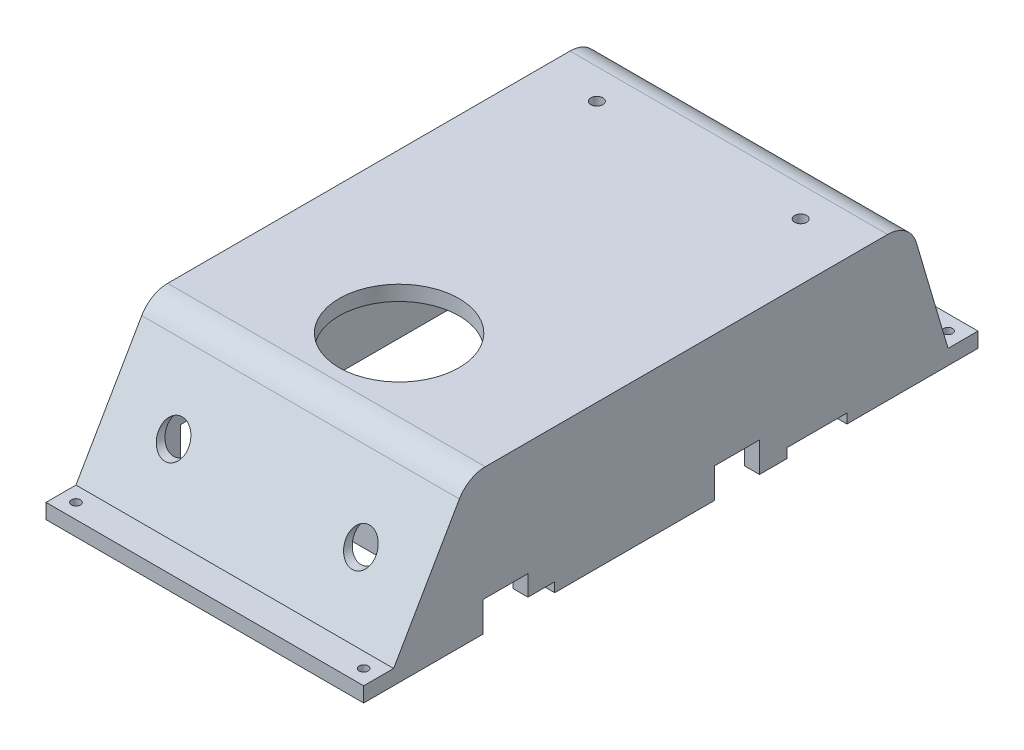
SolidWorks part; units mm, degrees
ref_plane "Front Plane" through (0, 0, 0) normal (0, 0, 1) x (1, 0, 0)
ref_plane "Top Plane" through (0, 0, 0) normal (0, 1, 0) x (1, 0, 0)
ref_plane "Right Plane" through (0, 0, 0) normal (1, 0, 0) x (0, 0, -1)
sketch "Sketch1" plane through (0, 0, 0) normal (0, 1, 0) x (1, 0, 0)
  line L1 (-78, -130) -> (78, -130)
  line L2 (-78, -130) -> (-78, 130)
  line L3 (-78, 130) -> (78, 130)
  line L4 (78, -130) -> (78, 130)
  line L5 (-78, -130) -> (78, 130) construction
  line L6 (-78, 130) -> (78, -130) construction
  point P1 (0, 0)
  dimension "D1" = 156
  dimension "D2" = 260
extrude "Boss-Extrude1" add sketch "Sketch1" along normal blind 10
sketch "Sketch2" plane through (0, 0, 0) normal (0, -1, 0) x (1, 0, 0)
  line L0 (78, 130) -> (78, -130) construction
  line L1 (-73, -120) -> (73, -120) construction
  line L2 (-73, -120) -> (-73, 125)
  line L3 (-73, 125) -> (73, 125)
  line L4 (73, -120) -> (73, 125)
  line L5 (78, -130) -> (-78, -130) construction
  line L7 (-78, -130) -> (-78, 130) construction
  line L8 (-78, 130) -> (78, 130) construction
  line L9 (78, 130) -> (78, -120)
  line L10 (-78, -120) -> (-78, 130)
  line L11 (-78, 130) -> (78, 130)
  line L12 (-73, -120) -> (-78, -120)
  line L13 (73, -120) -> (78, -120)
  point P0 (0, 0)
  dimension "D1" = 5
  dimension "D2" = 5
  dimension "D3" = 10
  dimension "D4" = 5
extrude "Boss-Extrude2" add sketch "Sketch2" along normal blind 66
sketch "Sketch3" plane through (0, 10, 0) normal (0, 1, 0) x (1, 0, 0)
  line L0 (-78, 130) -> (-78, -130) construction
  line L2 (-73, -125) -> (73, -125) construction
  circle A0 centre (0, -70) radius 40
  dimension "D2" = 80
  dimension "D1" = 55
  dimension "D3" = 78
extrude "Cut-Extrude1" cut sketch "Sketch3" against normal through all
sketch "Sketch4" plane through (0, 0, 130) normal (0, 0, 1) x (1, 0, 0)
  line L0 (0, 10) -> (0, -66) construction
  line L1 (-78, 10) -> (78, 10) construction
  line L2 (78, -66) -> (-78, -66) construction
  line L3 (-72.5, -28.5) -> (-52.5, -28.5)
  line L4 (-52.5, -28.5) -> (-52.5, -66)
  line L5 (-52.5, -66) -> (-72.5, -66)
  line L6 (-72.5, -66) -> (-72.5, -28.5)
  line L7 (52.5, -66) -> (72.5, -66)
  line L8 (52.5, -28.5) -> (52.5, -66)
  line L9 (72.5, -28.5) -> (52.5, -28.5)
  line L10 (72.5, -66) -> (72.5, -28.5)
  line L11 (-78, 10) -> (-78, -66) construction
  dimension "D1" = 20
  dimension "D2" = 37.5
  dimension "D3" = 5.5
extrude "Cut-Extrude2" cut sketch "Sketch4" against normal blind 5
sketch "Sketch6" plane through (0, -66, 0) normal (0, -1, 0) x (1, 0, 0)
  line L0 (78, 130) -> (72.5, 130) construction
  line L1 (-7.5, 145) -> (7.5, 145)
  line L2 (-7.5, 145) -> (-7.5, 130)
  line L3 (-7.5, 130) -> (7.5, 130)
  line L4 (7.5, 145) -> (7.5, 130)
  line L5 (-7.5, 145) -> (7.5, 130) construction
  line L6 (-7.5, 130) -> (7.5, 145) construction
  line L7 (-78, 130) -> (-78, -120) construction
  point P0 (0, 137.5)
  dimension "D1" = 15
  dimension "D2" = 15
  dimension "D3" = 78
extrude "Boss-Extrude3" add sketch "Sketch6" against normal blind 10
sketch "Sketch7" plane through (0, -66, 0) normal (0, -1, 0) x (1, 0, 0)
  line L0 (7.5, 145) -> (-7.5, 145) construction
  line L1 (-7.5, 145) -> (-7.5, 130) construction
  circle A0 centre (0, 137.5) radius 4
  dimension "D1" = 8
  dimension "D2" = 7.5
  dimension "D3" = 7.5
extrude "Cut-Extrude4" cut sketch "Sketch7" against normal blind 10
fillet "Fillet1" radius 2 2 edges at (7.5, -61, 145) (-7.5, -61, 145)
sketch "Sketch8" plane through (0, 0, -130) normal (0, 0, -1) x (-1, 0, 0)
  line L4 (-78, 0) -> (78, 0)
  line L5 (78, 0) -> (78, 10)
  line L6 (78, 10) -> (-78, 10)
  line L9 (78, 0) -> (78, 10)
  line L10 (78, 10) -> (-78, 10)
  line L12 (-78, 0) -> (78, 0)
  line L14 (-78, 10) -> (-78, 0)
  line L15 (-78, 10) -> (-78, 0)
  dimension "D1" = 0
extrude "Boss-Extrude4" add sketch "Sketch8" along normal blind 10
sketch "Sketch9" plane through (0, 10, 0) normal (0, 1, 0) x (1, 0, 0)
  line L0 (-78, 140) -> (78, 140) construction
  line L1 (-78, 140) -> (-78, -130) construction
  line L2 (78, -130) -> (78, 140) construction
  circle A0 centre (-68, 130) radius 4
  circle A1 centre (68, 130) radius 4
  dimension "D1" = 8
  dimension "D6" = 8
  dimension "D2" = 10
  dimension "D3" = 10
  dimension "D4" = 10
  dimension "D5" = 10
extrude "Cut-Extrude5" cut sketch "Sketch9" against normal through all
sketch "Sketch10" plane through (0, 0, -140) normal (0, 0, -1) x (-1, 0, 0)
  line L4 (-78, 10) -> (-78, 0)
  line L5 (-78, 0) -> (78, 0)
  line L6 (78, 0) -> (78, 10)
  line L7 (78, 10) -> (-78, 10)
  line L8 (-78, 10) -> (-78, 0)
  line L9 (-78, 0) -> (78, 0)
  line L10 (78, 0) -> (78, 10)
  line L11 (78, 10) -> (-78, 10)
  dimension "D1" = 0
extrude "Boss-Extrude5" add sketch "Sketch10" along normal blind 25
sketch "Sketch11" plane through (0, 10, 0) normal (0, 1, 0) x (1, 0, 0)
  line L0 (0, -145) -> (0, 165) construction
  line L1 (-78, 165) -> (-106, 165)
  line L2 (-78, 165) -> (-78, -130)
  line L3 (-78, -130) -> (-106, -130)
  line L4 (-106, 165) -> (-106, -130)
  line L5 (5.5, -145) -> (-5.5, -145) construction
  line L6 (-78, 165) -> (78, 165) construction
  line L7 (78, -130) -> (106, -130)
  line L8 (106, 165) -> (106, -130)
  line L9 (78, 165) -> (106, 165)
  line L10 (78, 165) -> (78, -130)
  dimension "D1" = 28
  dimension "D2" = 295
extrude "Boss-Extrude6" add sketch "Sketch11" against normal up to surface (10 mm away) up to face at (-68, 0, -134)
sketch "Sketch12" plane through (-106, 0, 0) normal (-1, 0, 0) x (0, 0, 1)
  line L0 (-165, 0) -> (-190.35, -86)
  line L1 (-165, 0) -> (130, 0) construction
  line L2 (-190.35, -86) -> (-210.35, -86)
  line L3 (-210.35, -86) -> (-210.35, -76)
  line L4 (-165, 10) -> (-190.35, -76)
  line L5 (-190.35, -76) -> (-210.35, -76)
  line L8 (-165, 10) -> (-165, 0)
  dimension "D1" = 73.576
  dimension "D2" = 86
  dimension "D3" = 10
  dimension "D4" = 20
  dimension "D5" = 20
extrude "Boss-Extrude7" add sketch "Sketch12" against normal up to surface (212 mm away) up to face at (106, 5, -17.5)
sketch "Sketch13" plane through (0, -76, 0) normal (0, 1, 0) x (1, 0, 0)
  line L0 (-106, 190.35) -> (-106, 210.35) construction
  line L1 (0, 210.35) -> (0, 190.35) construction
  line L2 (106, 210.35) -> (-106, 210.35) construction
  line L3 (106, 190.35) -> (-106, 190.35) construction
  circle A0 centre (-96, 200.35) radius 3
  circle A1 centre (96, 200.35) radius 3
  dimension "D2" = 6
  dimension "D1" = 10
  dimension "D3" = 10
extrude "Cut-Extrude6" cut sketch "Sketch13" against normal through all
sketch "Sketch17" plane through (106, 0, 0) normal (1, 0, 0) x (0, 0, -1)
  line L0 (-130, 0) -> (-179.6521, -86)
  line L1 (120, 0) -> (-130, 0) construction
  line L2 (-179.6521, -86) -> (-199.6521, -86)
  line L3 (-199.6521, -86) -> (-199.6521, -76)
  line L4 (-199.6521, -76) -> (-179.6521, -76)
  line L5 (-130, 10) -> (-179.6521, -76)
  line L6 (-130, 10) -> (-130, 0)
  dimension "D1" = 60
  dimension "D2" = 86
  dimension "D3" = 10
  dimension "D4" = 20
extrude "Boss-Extrude10" add sketch "Sketch17" against normal up to surface (212 mm away) up to face at (-106, -38, -108.925)
sketch "Sketch18" plane through (0, -76, 0) normal (0, 1, 0) x (1, 0, 0)
  line L0 (-106, -179.6521) -> (-106, -199.6521) construction
  line L1 (0, -179.6521) -> (0, -199.6521) construction
  line L2 (-106, -179.6521) -> (106, -179.6521) construction
  line L3 (-106, -199.6521) -> (106, -199.6521) construction
  circle A0 centre (-96, -189.6521) radius 3
  circle A1 centre (96, -189.6521) radius 3
  dimension "D1" = 6
  dimension "D2" = 10
  dimension "D3" = 10
extrude "Cut-Extrude8" cut sketch "Sketch18" against normal through all
sketch "Sketch19" plane through (0, 0, 130) normal (0, 0, 1) x (1, 0, 0)
  line L0 (-52.5, -28.5) -> (-72.5, -28.5) construction
  line L1 (0, -66) -> (0, 0) construction
  line L2 (5.5, -66) -> (-5.5, -66) construction
  line L3 (-106, 10) -> (-106, -76) construction
  circle A0 centre (-62.5, -38.5) radius 10
  circle A1 centre (62.5, -38.5) radius 10
  dimension "D1" = 20
  dimension "D2" = 10
  dimension "D3" = 43.5
extrude "Cut-Extrude9" cut sketch "Sketch19" along normal blind 113
ref_plane "Plane3" through (0, 0, -165) normal (0, 0, -1) x (-1, 0, 0)
sketch "Sketch20" plane through (0, 0, -165) normal (0, 0, -1) x (-1, 0, 0)
  line L0 (-106, 0) -> (106, 0) construction
  line L1 (-106, -86) -> (-96, -86)
  line L2 (-106, -86) -> (-106, 0)
  line L3 (-106, 0) -> (-96, 0)
  line L4 (-96, -86) -> (-96, 0)
  line L5 (0, 0) -> (0, -76) construction
  line L6 (-106, -76) -> (106, -76) construction
  line L7 (106, -86) -> (96, -86)
  line L8 (106, -86) -> (106, 0)
  line L9 (106, 0) -> (96, 0)
  line L10 (96, -86) -> (96, 0)
  dimension "D1" = 10
extrude "Boss-Extrude11" add sketch "Sketch20" along normal up to surface and the other way up to surface up to face at (0, -33, -177.675) other way up to face at (-62.5, -28.5, 152.228)
fillet "Fillet2" radius 20 2 edges at (0, 10, -165) (0, 10, 130)
sketch "Sketch21" plane through (78, 0, 0) normal (1, 0, 0) x (0, 0, -1)
  line L1 (120, -66) -> (120, 0) construction
  line L2 (165, 0) -> (-130, 0) construction
  circle A0 centre (90, -30.5) radius 15
  dimension "D1" = 30
  dimension "D2" = 30
  dimension "D3" = 30.5
extrude "Cut-Extrude11" cut sketch "Sketch21" against normal up to surface (5 mm away) up to face at (73, -33, 2.5)
sketch "Sketch22" plane through (106, 0, 0) normal (1, 0, 0) x (0, 0, -1)
  line L0 (120, -66) -> (-130, -66) construction
  line L1 (-120, -66) -> (-90, -66)
  line L2 (-120, -66) -> (-120, -86)
  line L3 (-120, -86) -> (-90, -86)
  line L4 (-90, -66) -> (-90, -86)
  line L5 (210.35, -86) -> (-199.6521, -86) construction
  line L6 (-130, 0) -> (-130, -66) construction
  line L7 (120, -66) -> (120, 0) construction
  line L8 (64.5, -66) -> (34.5, -66)
  line L9 (64.5, -66) -> (64.5, -86)
  line L10 (64.5, -86) -> (34.5, -86)
  line L11 (34.5, -66) -> (34.5, -86)
  dimension "D1" = 10
  dimension "D2" = 30
  dimension "D3" = 55.5
  dimension "D4" = 30
extrude "Cut-Extrude12" cut sketch "Sketch22" against normal through all both and the other way through all
sketch "Sketch23" plane through (-106, 0, 0) normal (-1, 0, 0) x (0, 0, 1)
  line L0 (-210.35, -86) -> (-64.5, -86) construction
  line L1 (-122.85, -86) -> (-82.85, -86)
  line L2 (-122.85, -86) -> (-122.85, -79.65)
  line L3 (-122.85, -79.65) -> (-82.85, -79.65)
  line L4 (-82.85, -86) -> (-82.85, -79.65)
  line L5 (-210.35, -76) -> (-210.35, -86) construction
  line L11 (-34.5, -86) -> (90, -86) construction
  line L12 (72.15, -86) -> (112.15, -86)
  line L13 (72.15, -86) -> (72.15, -79.65)
  line L14 (72.15, -79.65) -> (112.15, -79.65)
  line L15 (112.15, -86) -> (112.15, -79.65)
  dimension "D1" = 87.5
  dimension "D2" = 40
  dimension "D3" = 6.35
  dimension "D4" = 155
  dimension "D5" = 40
  dimension "D6" = 6.35
extrude "Cut-Extrude13" cut sketch "Sketch23" against normal through all both
equation "\"t_wall\"= 5mm"
